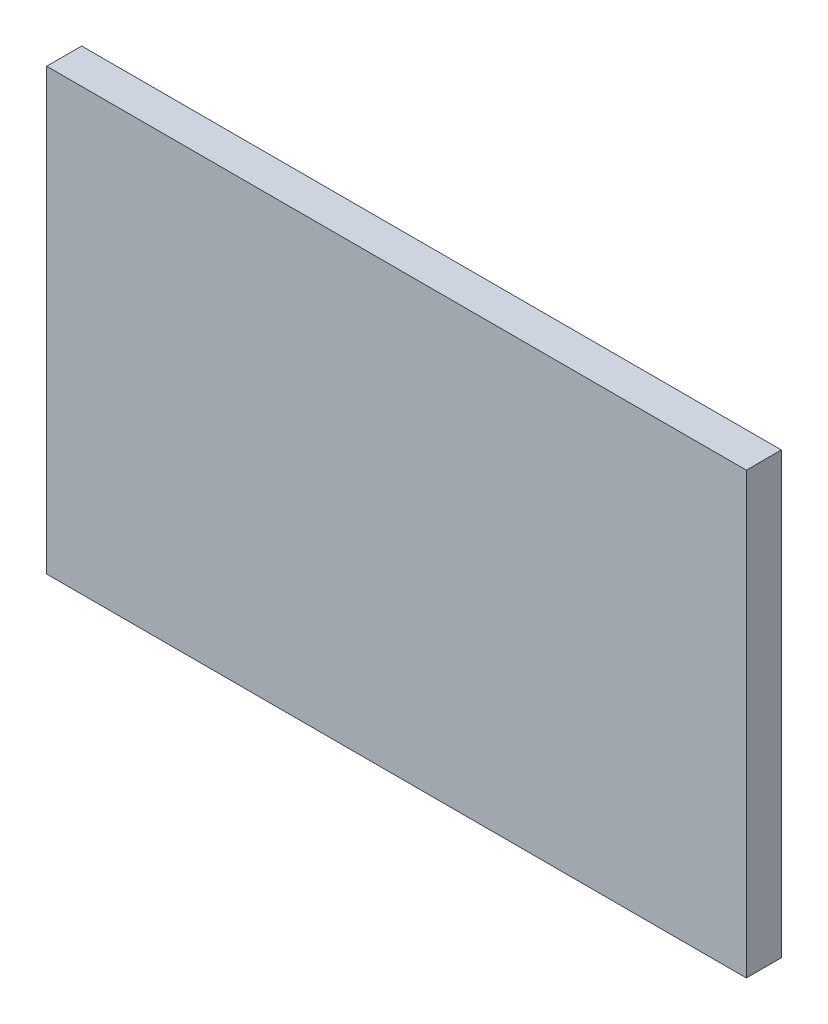
SolidWorks part; units mm, degrees
ref_plane "Front Plane" through (0, 0, 0) normal (0, 0, 1) x (1, 0, 0)
ref_plane "Top Plane" through (0, 0, 0) normal (0, 1, 0) x (1, 0, 0)
ref_plane "Right Plane" through (0, 0, 0) normal (1, 0, 0) x (0, 0, -1)
sketch "Sketch1" plane through (0, 0, 0) normal (0, 0, 1) x (1, 0, 0)
  line L1 (14, 8.8) -> (-14, 8.8)
  line L2 (14, 8.8) -> (14, -8.8)
  line L3 (14, -8.8) -> (-14, -8.8)
  line L4 (-14, 8.8) -> (-14, -8.8)
  line L5 (14, 8.8) -> (-14, -8.8) construction
  line L6 (14, -8.8) -> (-14, 8.8) construction
  point P0 (0, 0)
  dimension "D1" = 17.6
  dimension "D2" = 28
extrude "Boss-Extrude1" add sketch "Sketch1" along normal blind 1.4
